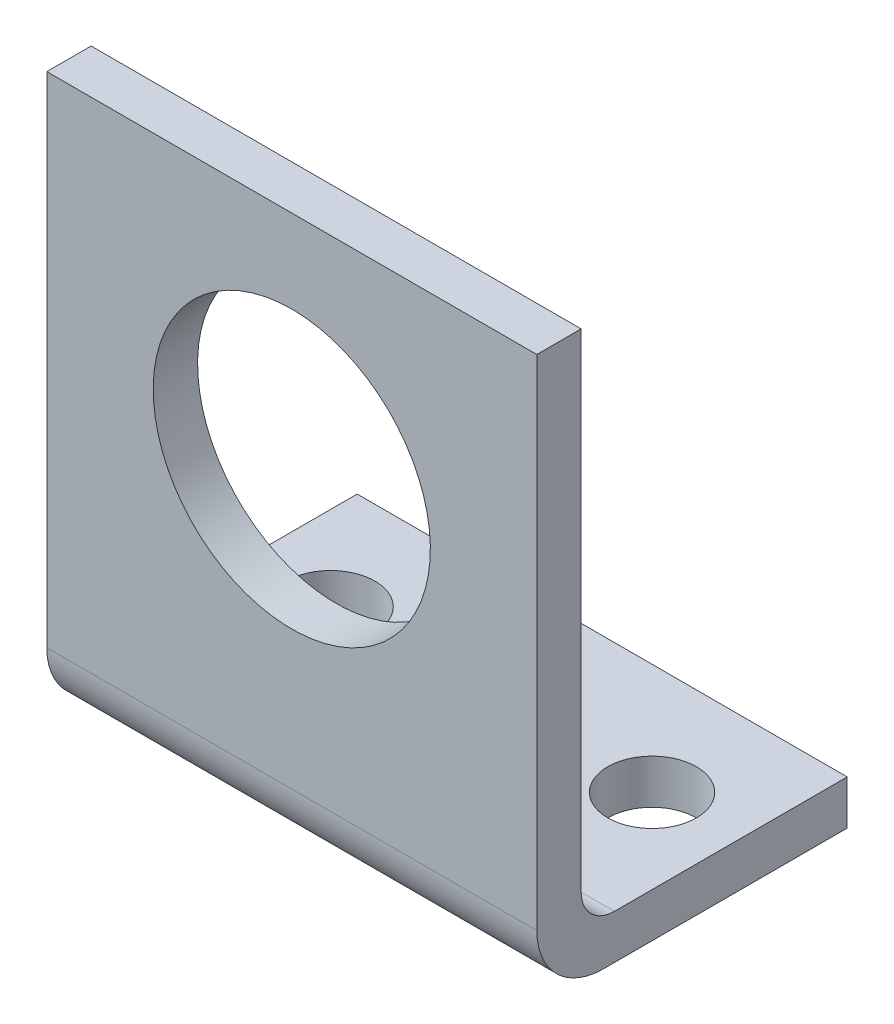
SolidWorks part; units mm, degrees
material "AISI 1020"
ref_plane "Plan de face" through (0, 0, 0) normal (0, 0, 1) x (1, 0, 0)
ref_plane "Plan de dessus" through (0, 0, 0) normal (0, 1, 0) x (1, 0, 0)
ref_plane "Plan de droite" through (0, 0, 0) normal (1, 0, 0) x (0, 0, -1)
sketch "Esquisse1" plane through (0, 0, 0) normal (1, 0, 0) x (0, 0, -1)
  line L0 (0, 25.5) -> (0, 3)
  line L1 (3, 0) -> (14, 0)
  line L2 (2, 25.5) -> (2, 3.5)
  line L3 (3.5, 2) -> (14, 2)
  line L4 (0, 25.5) -> (2, 25.5)
  line L5 (14, 2) -> (14, 0)
  line L6 (2, 25.5) -> (2, 2) construction
  line L7 (2, 2) -> (14, 2) construction
  line L8 (0, 25.5) -> (0, 0) construction
  line L9 (0, 0) -> (14, 0) construction
  arc A0 (2, 3.5) -> (3.5, 2) centre (3.5, 3.5) ccw
  arc A1 (0, 3) -> (3, 0) centre (3, 3) ccw
  point P13 (0, 0)
  dimension "D4" = 1.5
  dimension "D5" = 3
  dimension "D1" = 14
  dimension "D2" = 25.5
  dimension "D3" = 2
extrude "Boss.-Extru.1" add sketch "Esquisse1" along normal blind 22.1
sketch "Esquisse2" plane through (0, 2, 0) normal (0, 1, 0) x (1, 0, 0)
  line L0 (22.1, 14) -> (0, 14) construction
  circle A0 centre (3.8, 9) radius 2
  circle A1 centre (18.3, 9) radius 2
  point P6 (11.05, 14)
  dimension "D3" = 4
  dimension "D1" = 14.5
  dimension "D2" = 5
  dimension "D4" = 7.25
extrude "Enlèv. mat.-Extru.1" cut sketch "Esquisse2" against normal through all
sketch "Esquisse3" plane through (0, 0, -2) normal (0, 0, -1) x (-1, 0, 0)
  line L0 (-22.1, 25.5) -> (0, 25.5) construction
  line L1 (-11.05, 0) -> (-11.05, 28.3442) construction
  line L2 (-22.1, 0) -> (0, 0) construction
  circle A0 centre (-11.05, 15.5) radius 6.25
  dimension "D2" = 12.5
  dimension "D1" = 10
extrude "Enlèv. mat.-Extru.2" cut sketch "Esquisse3" against normal through all
